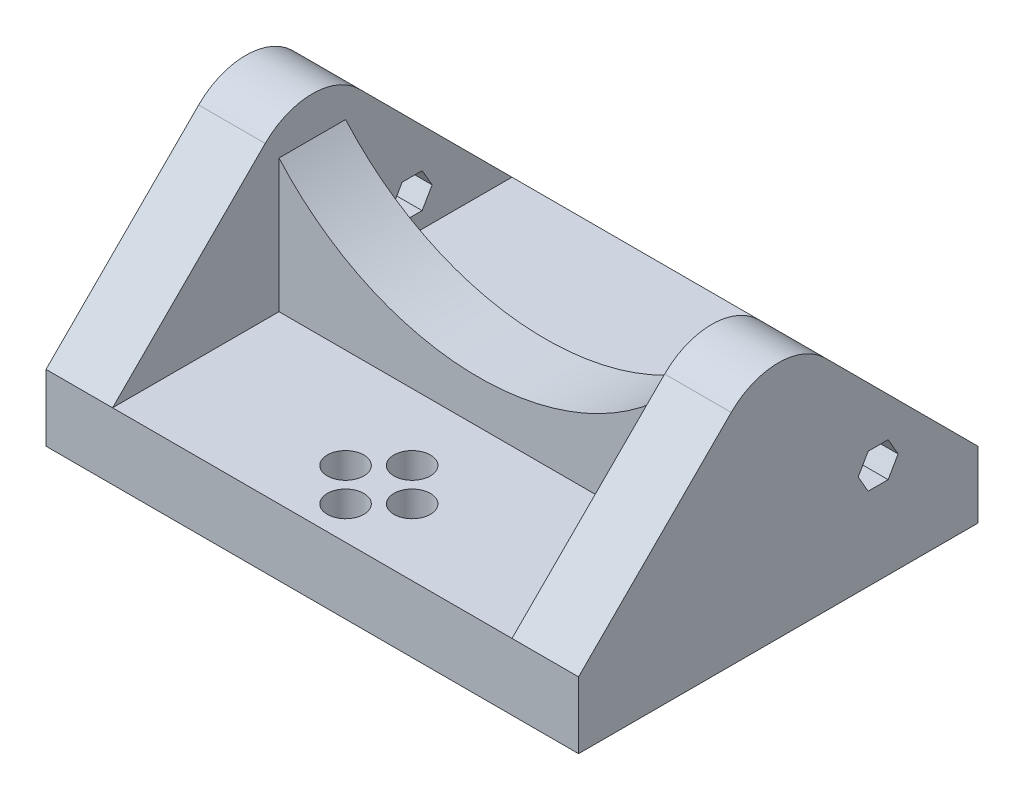
SolidWorks part; units mm, degrees
material "Commercially Pure CP-Ti UNS R50400 (SS)"
ref_plane "Front Plane" through (0, 0, 0) normal (0, 0, 1) x (1, 0, 0)
ref_plane "Top Plane" through (0, 0, 0) normal (0, 1, 0) x (1, 0, 0)
ref_plane "Right Plane" through (0, 0, 0) normal (1, 0, 0) x (0, 0, -1)
sketch "Sketch1" plane through (0, 0, 0) normal (0, 1, 0) x (1, 0, 0)
  line L1 (0, 0) -> (80, 0)
  line L2 (0, 0) -> (0, 60)
  line L3 (0, 60) -> (80, 60)
  line L4 (80, 0) -> (80, 60)
  dimension "D1" = 80
  dimension "D2" = 60
extrude "Boss-Extrude1" add sketch "Sketch1" along normal blind 10 contours L2 L3 L4 L1
sketch "Sketch2" plane through (0, 0, 0) normal (1, 0, 0) x (0, 0, -1)
  line L0 (0, 10) -> (30, 40)
  line L1 (30, 40) -> (60, 10)
  line L2 (60, 10) -> (0, 10)
  point P3 (0, 0)
  point P6 (30, 10)
  point P7 (0, 0)
  dimension "D1" = 45
extrude "Boss-Extrude2" add sketch "Sketch2" along normal blind 10 contours L2 L0 L1
pattern_linear "LPattern1" count 2 spacing 70 along (1, 0, 0) of "Boss-Extrude2"
sketch "Sketch3" plane through (0, 0, 0) normal (0, 0, 1) x (1, 0, 0)
  line L0 (10, 10) -> (10, 40) construction
  line L1 (70, 10) -> (70, 40) construction
  line L2 (10, 30) -> (10, 10)
  line L3 (10, 10) -> (70, 10) construction
  line L4 (10, 10) -> (70, 10)
  line L5 (80, 10) -> (70, 10) construction
  line L6 (70, 10) -> (70, 30)
  arc A0 (10, 30) -> (70, 30) centre (40, 56.4575) ccw
  dimension "D1" = 40
  dimension "D2" = 20
extrude "Boss-Extrude3" add sketch "Sketch3" along normal mid plane 10 from vertex at -30 contours A0 L6 L4 L2 starting at point (10, 40, -30)
fillet "Fillet1" radius 10 2 edges at (75, 40, -30) (5, 40, -30)
sketch "Sketch4" plane through (0, 10, 0) normal (0, 1, 0) x (1, 0, 0)
  line L0 (10, 0) -> (70, 0) construction
  line L2 (0, 0) -> (0, 22.9289) construction
  circle A0 centre (40, 10) radius 5 construction
  circle A1 centre (40, 15) radius 2.7392
  circle A2 centre (45, 10) radius 2.7392
  circle A3 centre (40, 5) radius 2.7392
  circle A4 centre (35, 10) radius 2.7392
  point P17 (40, 10)
  dimension "D3" = 10
  dimension "D5" = 5.4784
  dimension "D1" = 10
  dimension "D2" = 40
  dimension "D4" = 4
extrude "Cut-Extrude1" cut sketch "Sketch4" against normal through all
sketch "Sketch5" plane through (0, 0, 0) normal (1, 0, 0) x (0, 0, -1)
  line L0 (0, 0) -> (60, 0) construction
  line L1 (46.5, 12.4019) -> (48, 15)
  line L2 (48, 15) -> (46.5, 17.5981)
  line L3 (46.5, 17.5981) -> (43.5, 17.5981)
  line L4 (43.5, 17.5981) -> (42, 15)
  line L5 (42, 15) -> (43.5, 12.4019)
  line L6 (43.5, 12.4019) -> (46.5, 12.4019)
  circle A0 centre (45, 15) radius 2.5981 construction
  arc A1 (37.0711, 32.9289) -> (22.9289, 32.9289) centre (30, 25.8579) ccw construction
  point P10 (0, 0)
  point P14 (0, 0)
  dimension "D1" = 15
  dimension "D2" = 3
  dimension "D3" = 15
extrude "Cut-Extrude2" cut sketch "Sketch5" along normal through all
